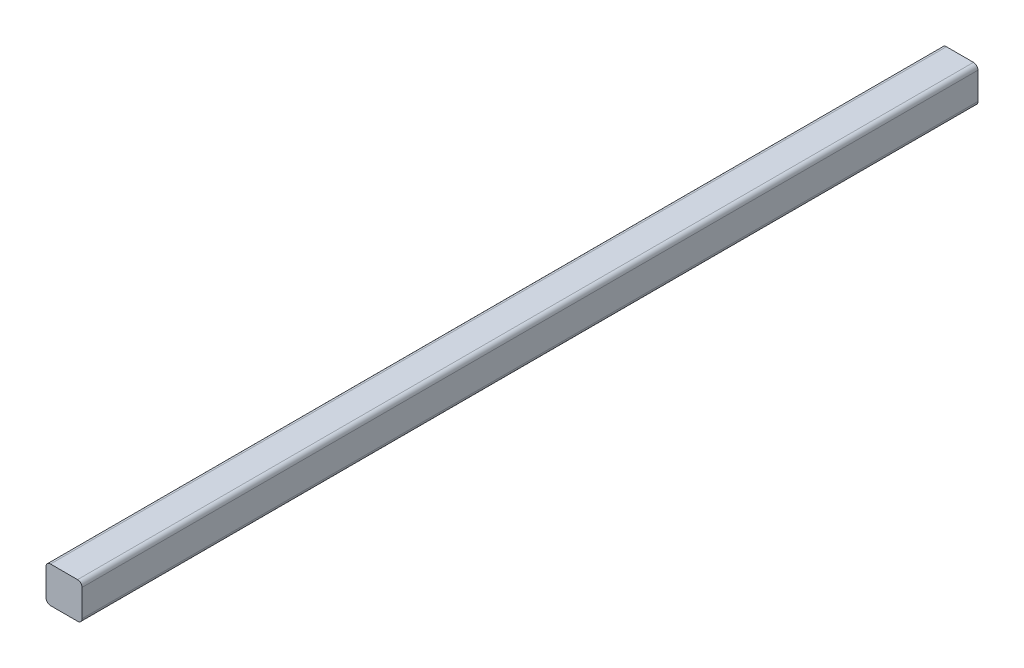
SolidWorks part; units mm, degrees
material "Pine"
ref_plane "Front Plane" through (0, 0, 0) normal (0, 0, 1) x (1, 0, 0)
ref_plane "Top Plane" through (0, 0, 0) normal (0, 1, 0) x (1, 0, 0)
ref_plane "Right Plane" through (0, 0, 0) normal (1, 0, 0) x (0, 0, -1)
sketch "Sketch1" plane through (0, 0, 0) normal (0, 0, 1) x (1, 0, 0)
  line L0 (-585.9322, 477.1947) -> (-550.9138, 477.1947) construction
  line L1 (-585.9322, 515.2947) -> (-547.8322, 515.2947)
  line L2 (-585.9322, 515.2947) -> (-585.9322, 477.1947)
  line L3 (-585.9322, 477.1947) -> (-547.8322, 477.1947)
  line L4 (-547.8322, 515.2947) -> (-547.8322, 477.1947)
  line L5 (-547.8322, 465.6941) -> (-547.8322, 515.2947) construction
extrude "Boss-Extrude1" add sketch "Sketch1" against normal up to surface (946.6588 mm away)
fillet "Fillet1" radius 4.7625 4 edges at (-585.9322, 515.2947, -473.3294) (-585.9322, 477.1947, -473.3294) (-547.8322, 477.1947, -473.3294) (-547.8322, 515.2947, -473.3294)
